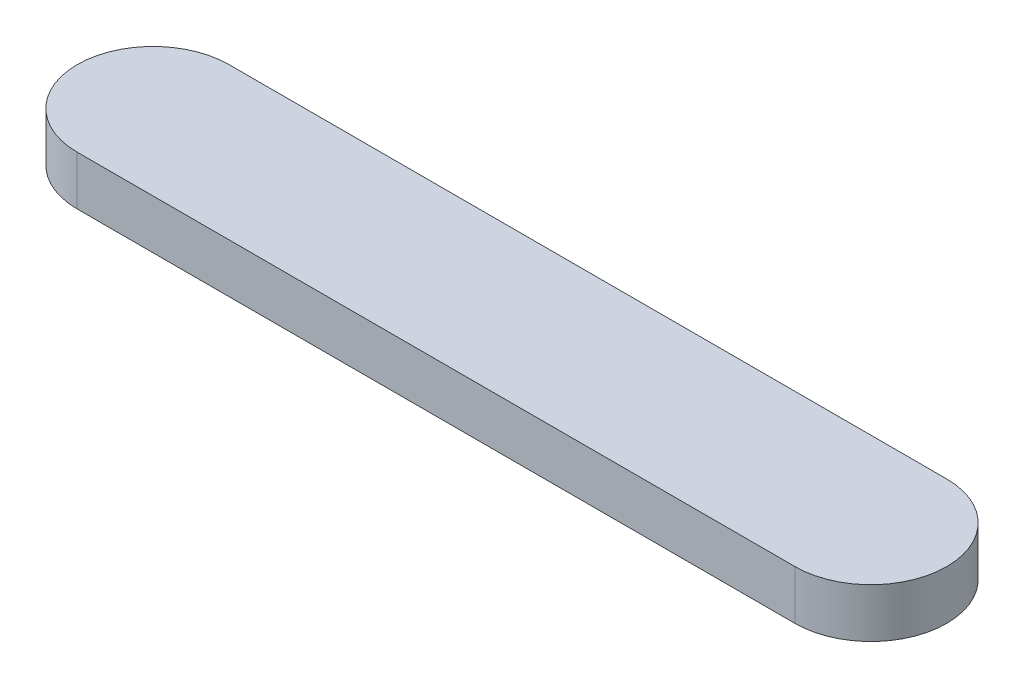
SolidWorks part; units mm, degrees
ref_plane "Front Plane" through (0, 0, 0) normal (0, 0, 1) x (1, 0, 0)
ref_plane "Top Plane" through (0, 0, 0) normal (0, 1, 0) x (1, 0, 0)
ref_plane "Right Plane" through (0, 0, 0) normal (1, 0, 0) x (0, 0, -1)
sketch "Sketch1" plane through (0, 0, 0) normal (0, 1, 0) x (1, 0, 0)
  line L0 (0, 0) -> (70, 0) construction
  line L1 (0, 7.4) -> (70, 7.4)
  line L2 (0, -7.4) -> (70, -7.4)
  arc A0 (0, 7.4) -> (0, -7.4) centre (0, 0) ccw
  arc A1 (70, -7.4) -> (70, 7.4) centre (70, 0) ccw
  point P3 (35, 0)
  point P8 (-7.4, 0)
  point P9 (77.4, 0)
  dimension "D1" = 84.8
  dimension "D2" = 14.8
extrude "Boss-Extrude1" add sketch "Sketch1" along normal blind 4.8
